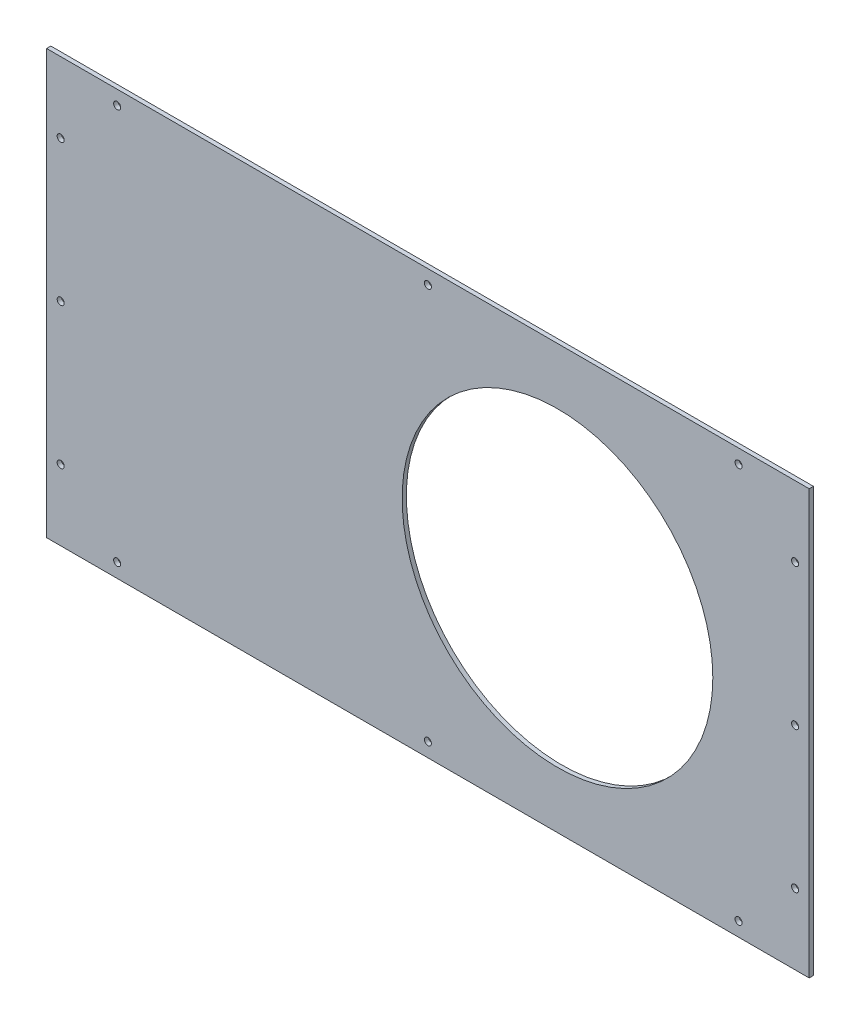
SolidWorks part; units mm, degrees
ref_plane "Alzado" through (0, 0, 0) normal (0, 0, 1) x (1, 0, 0)
ref_plane "Planta" through (0, 0, 0) normal (0, 1, 0) x (1, 0, 0)
ref_plane "Vista lateral" through (0, 0, 0) normal (1, 0, 0) x (0, 0, -1)
sketch "Croquis1" plane through (0, 0, 0) normal (0, 0, 1) x (1, 0, 0)
  line L1 (-270, 150) -> (270, 150)
  line L2 (-270, 150) -> (-270, -150)
  line L3 (-270, -150) -> (270, -150)
  line L4 (270, 150) -> (270, -150)
  line L5 (-270, 150) -> (270, -150) construction
  line L6 (-270, -150) -> (270, 150) construction
  point P0 (0, 0)
  dimension "D1" = 540
  dimension "D2" = 300
extrude "Saliente-Extruir1" add sketch "Croquis1" along normal blind 3
sketch "Croquis2" plane through (0, 0, 3) normal (0, 0, 1) x (1, 0, 0)
  line L0 (-270, 150) -> (-270, -150) construction
  line L1 (-260, -140) -> (260, -140) construction
  line L2 (-260, -140) -> (-260, 140) construction
  line L3 (-260, 140) -> (260, 140) construction
  line L4 (260, -140) -> (260, 140) construction
  line L5 (-260, -140) -> (260, 140) construction
  line L6 (-260, 140) -> (260, -140) construction
  line L7 (270, 150) -> (-270, 150) construction
  line L8 (-260, 0) -> (260, 0) construction
  line L9 (0, 140) -> (0, -140) construction
  circle A0 centre (0, 140) radius 2.5
  circle A1 centre (-220, 140) radius 2.5
  circle A2 centre (-260, 0) radius 2.5
  circle A3 centre (-260, 100) radius 2.5
  circle A4 centre (-260, -100) radius 2.5
  circle A5 centre (220, 140) radius 2.5
  circle A6 centre (260, -100) radius 2.5
  circle A7 centre (260, 0) radius 2.5
  circle A8 centre (260, 100) radius 2.5
  circle A9 centre (220, -140) radius 2.5
  circle A10 centre (0, -140) radius 2.5
  circle A11 centre (-220, -140) radius 2.5
  point P0 (0, 0)
  dimension "D3" = 5
  dimension "D5" = 220
  dimension "D7" = 100
  dimension "D1" = 10
  dimension "D2" = 10
  dimension "D4" = 2
  dimension "D6" = 2
extrude "Cortar-Extruir1" cut sketch "Croquis2" against normal through all
sketch "Croquis3" plane through (0, 0, 3) normal (0, 0, 1) x (1, 0, 0)
  circle A0 centre (91.7562, 0) radius 110
  point P2 (91.7562, 0)
  dimension "D1" = 220
extrude "Cortar-Extruir2" cut sketch "Croquis3" against normal through all contours A0
